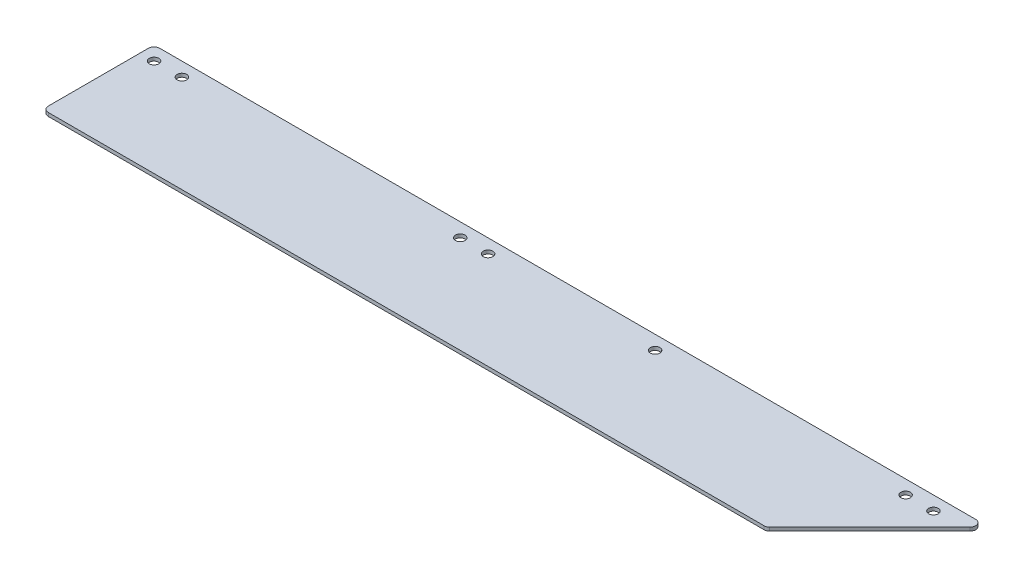
SolidWorks part; units mm, degrees
ref_plane "Front Plane" through (0, 0, 0) normal (0, 0, 1) x (1, 0, 0)
ref_plane "Top Plane" through (0, 0, 0) normal (0, 1, 0) x (1, 0, 0)
ref_plane "Right Plane" through (0, 0, 0) normal (1, 0, 0) x (0, 0, -1)
sketch "Sketch1" plane through (0, 0, 0) normal (0, 1, 0) x (1, 0, 0)
  line L0 (2.54, 0) -> (374.8679, 0)
  line L1 (376.6639, -4.3361) -> (330.9439, -50.0561)
  line L2 (329.1479, -50.8) -> (2.54, -50.8)
  line L3 (0, -48.26) -> (0, -2.54)
  arc A0 (376.6639, -4.3361) -> (374.8679, 0) centre (374.8679, -2.54) ccw
  arc A1 (330.9439, -50.0561) -> (329.1479, -50.8) centre (329.1479, -48.26) cw
  arc A2 (2.54, 0) -> (0, -2.54) centre (2.54, -2.54) ccw
  arc A3 (2.54, -50.8) -> (0, -48.26) centre (2.54, -48.26) cw
  circle A4 centre (6.35, -6.35) radius 2.1828
  circle A5 centre (19.05, -6.35) radius 2.1828
  circle A6 centre (146.05, -6.35) radius 2.1828
  circle A7 centre (158.75, -6.35) radius 2.1828
  circle A8 centre (349.25, -6.35) radius 2.1828
  circle A9 centre (361.95, -6.35) radius 2.1828
  circle A10 centre (234.95, -6.35) radius 2.1828
  point P7 (381, 0)
  point P10 (330.2, -50.8)
  point P13 (0, 0)
  point P16 (0, -50.8)
  point P31 (233.3174, -22.0391)
  dimension "D4" = 2.54
  dimension "D9" = 4.3656
  dimension "D10" = 4.3656
  dimension "D11" = 4.3656
  dimension "D12" = 4.3656
  dimension "D16" = 12.7
  dimension "D18" = 4.3656
  dimension "D22" = 4.3656
  dimension "D25" = 4.3656
  dimension "D1" = 50.8
  dimension "D2" = 381
  dimension "D3" = 330.2
  dimension "D5" = 6.35
  dimension "D6" = 6.35
  dimension "D7" = 6.35
  dimension "D8" = 12.7
  dimension "D13" = 6.35
  dimension "D14" = 6.35
  dimension "D15" = 127
  dimension "D17" = 6.35
  dimension "D19" = 190.5
  dimension "D20" = 12.7
  dimension "D21" = 6.35
  dimension "D23" = 76.2
  dimension "D24" = 0
extrude "Boss-Extrude1" add sketch "Sketch1" along normal blind 1.5875
